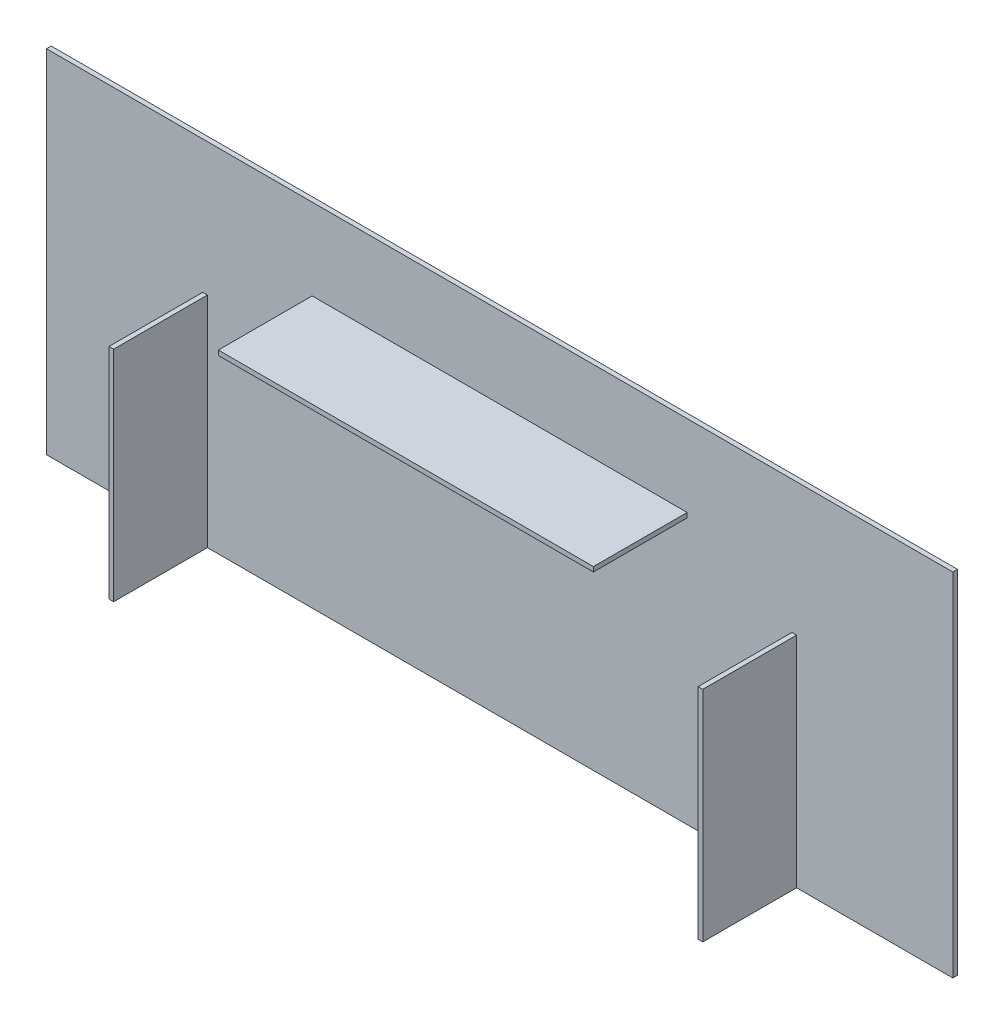
SolidWorks part; units mm, degrees
ref_plane "前基準面" through (0, 0, 0) normal (0, 0, 1) x (1, 0, 0)
ref_plane "上基準面" through (0, 0, 0) normal (0, 1, 0) x (1, 0, 0)
ref_plane "右基準面" through (0, 0, 0) normal (1, 0, 0) x (0, 0, -1)
sketch "草圖1" plane through (0, 0, 0) normal (0, 0, 1) x (1, 0, 0)
  line L1 (-177.0687, 82.7905) -> (112.9313, 82.7905)
  line L2 (-177.0687, 82.7905) -> (-177.0687, -29.7095)
  line L3 (-177.0687, -29.7095) -> (112.9313, -29.7095)
  line L4 (112.9313, 82.7905) -> (112.9313, -29.7095)
  dimension "D1" = 112.5
  dimension "D2" = 290
extrude "填料-伸長1" add sketch "草圖1" along normal blind 1.5 contours L2 L3 L4 L1
sketch "草圖2" plane through (0, 0, 1.5) normal (0, 0, 1) x (1, 0, 0)
  line L0 (-177.0687, -29.7095) -> (112.9313, -29.7095) construction
  line L1 (-92.0687, 56.7905) -> (27.9313, 56.7905)
  line L2 (-92.0687, 56.7905) -> (-92.0687, 55.2905)
  line L3 (-92.0687, 55.2905) -> (27.9313, 55.2905)
  line L4 (27.9313, 56.7905) -> (27.9313, 55.2905)
  line L6 (112.9313, 82.7905) -> (112.9313, -29.7095) construction
  line L7 (-177.0687, 82.7905) -> (-177.0687, -29.7095) construction
  line L8 (62.9313, -29.7095) -> (61.4313, -29.7095)
  line L9 (62.9313, -29.7095) -> (62.9313, 40.2905)
  line L10 (62.9313, 40.2905) -> (61.4313, 40.2905)
  line L11 (61.4313, -29.7095) -> (61.4313, 40.2905)
  line L12 (-125.5687, -29.7095) -> (-127.0687, -29.7095)
  line L13 (-125.5687, -29.7095) -> (-125.5687, 40.2905)
  line L14 (-125.5687, 40.2905) -> (-127.0687, 40.2905)
  line L15 (-127.0687, -29.7095) -> (-127.0687, 40.2905)
  point P18 (0, 0)
  point P19 (0, 0)
  dimension "D1" = 1.5
  dimension "D2" = 120
  dimension "D3" = 85
  dimension "D4" = 85
  dimension "D5" = 1.5
  dimension "D6" = 50
  dimension "D7" = 1.5
  dimension "D8" = 70
  dimension "D9" = 50
  dimension "D10" = 70
extrude "填料-伸長2" add sketch "草圖2" along normal blind 30 contours L13 L14 L15 L12 | L1 L4 L3 L2 | L9 L10 L11 L8
